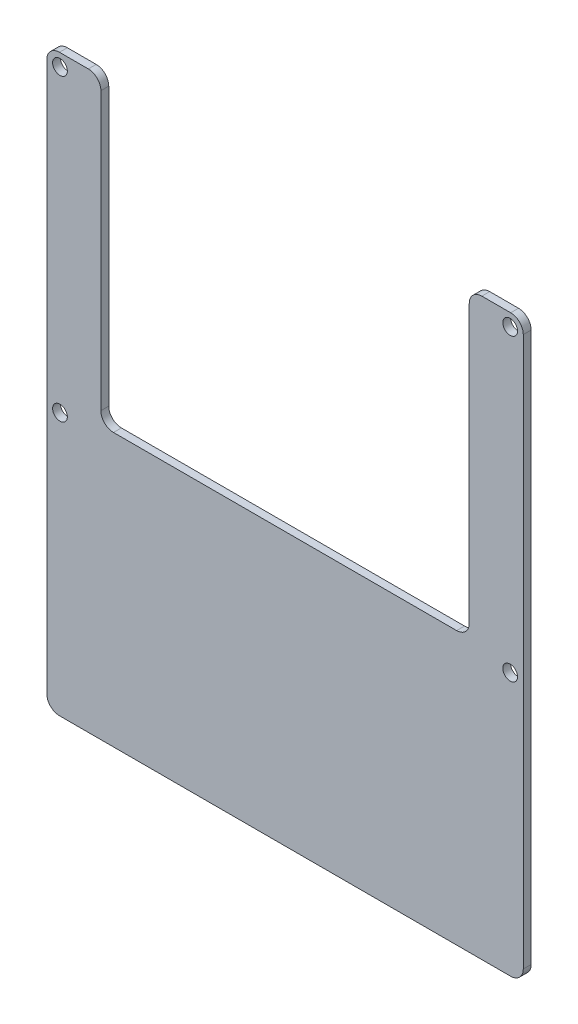
SolidWorks part; units mm, degrees
ref_plane "Front Plane" through (0, 0, 0) normal (0, 0, 1) x (1, 0, 0)
ref_plane "Top Plane" through (0, 0, 0) normal (0, 1, 0) x (1, 0, 0)
ref_plane "Right Plane" through (0, 0, 0) normal (1, 0, 0) x (0, 0, -1)
sketch "Sketch1" plane through (0, 0, 0) normal (0, 0, 1) x (1, 0, 0)
  line L0 (20, 20) -> (117, 20)
  line L1 (117, 20) -> (117, 137)
  line L2 (20, 137) -> (31, 137)
  line L3 (20, 137) -> (20, 20)
  line L4 (31, 137) -> (31, 75.46)
  line L5 (31, 75.46) -> (106, 75.46)
  line L6 (106, 75.46) -> (106, 137)
  line L7 (106, 137) -> (117, 137)
  line L8 (22.6657, 134.46) -> (114.3343, 134.46) construction
  circle A0 centre (22.6657, 134.46) radius 1.5
  circle A1 centre (114.3343, 134.46) radius 1.5
  circle A2 centre (22.6657, 73.5) radius 1.5
  circle A3 centre (114.3343, 73.5) radius 1.5
  point P12 (68.5, 134.46)
  point P13 (68.5, 75.46)
  point P19 (0, 0)
  point P20 (0, 0)
  point P21 (0, 0)
  dimension "D5" = 3
  dimension "D1" = 97
  dimension "D2" = 75
  dimension "D3" = 61.54
  dimension "D4" = 117
  dimension "D6" = 91.6686
  dimension "D7" = 2.54
  dimension "D8" = 20
  dimension "D9" = 20
  dimension "D10" = 60.96
extrude "Board" add sketch "Sketch1" along normal blind 1.6
fillet "Fillet1" radius 2.56 8 edges at (31, 137, 0.8) (31, 75.46, 0.8) (106, 75.46, 0.8) (106, 137, 0.8) (117, 137, 0.8) (117, 20, 0.8) (20, 20, 0.8) (20, 137, 0.8)
